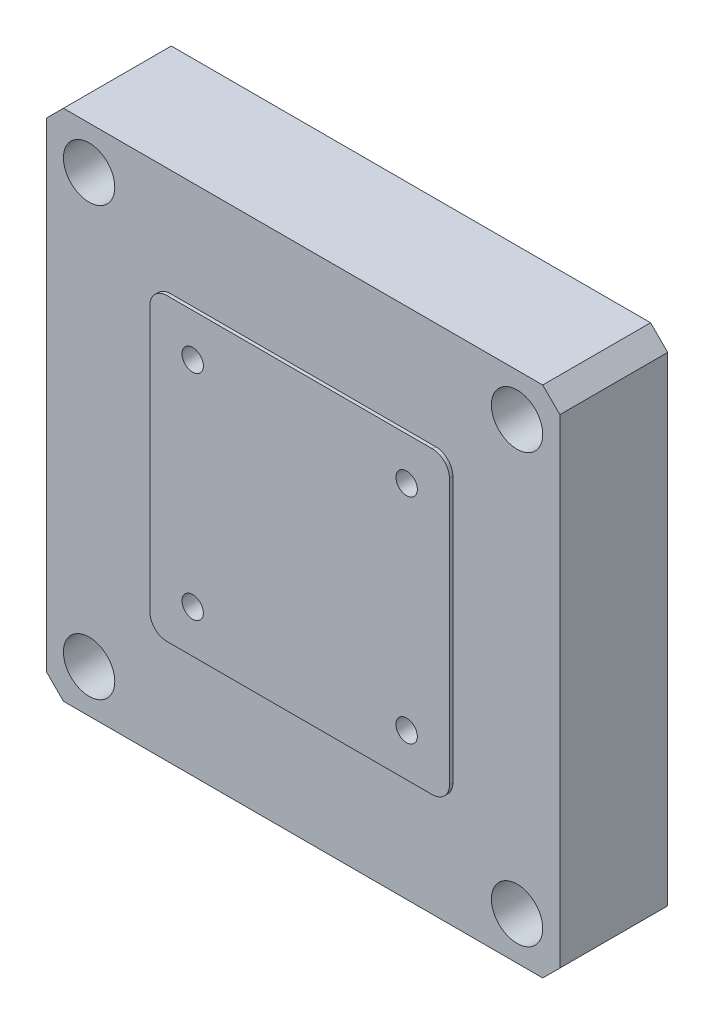
SolidWorks part; units mm, degrees
ref_plane "前视基准面" through (0, 0, 0) normal (0, 0, 1) x (1, 0, 0)
ref_plane "上视基准面" through (0, 0, 0) normal (0, 1, 0) x (1, 0, 0)
ref_plane "右视基准面" through (0, 0, 0) normal (1, 0, 0) x (0, 0, -1)
sketch "草图1" plane through (0, 0, 0) normal (0, 0, 1) x (1, 0, 0)
  line L1 (-30, 30) -> (30, 30)
  line L2 (-30, 30) -> (-30, -30)
  line L3 (-30, -30) -> (30, -30)
  line L4 (30, 30) -> (30, -30)
  line L5 (-30, 30) -> (30, -30) construction
  line L6 (-30, -30) -> (30, 30) construction
  point P0 (0, 0)
  dimension "D1" = 60
extrude "凸台-拉伸1" add sketch "草图1" along normal blind 12.6
chamfer "倒角1" distance 2 angle 45 4 edges at (-30, -30, 6.3) (30, -30, 6.3) (30, 30, 6.3) (-30, 30, 6.3)
sketch "草图2" plane through (0, 0, 12.6) normal (0, 0, 1) x (1, 0, 0)
  line L1 (-17.5, 17.5) -> (17.5, 17.5)
  line L2 (-17.5, 17.5) -> (-17.5, -17.5)
  line L3 (-17.5, -17.5) -> (17.5, -17.5)
  line L4 (17.5, 17.5) -> (17.5, -17.5)
  line L5 (-17.5, 17.5) -> (17.5, -17.5) construction
  line L6 (-17.5, -17.5) -> (17.5, 17.5) construction
  point P0 (0, 0)
  dimension "D1" = 35
extrude "凸台-拉伸2" add sketch "草图2" along normal blind 0.4
fillet "圆角1" radius 2 4 edges at (17.5, -17.5, 12.8) (-17.5, -17.5, 12.8) (17.5, 17.5, 12.8) (-17.5, 17.5, 12.8)
sketch "草图3" plane through (0, 0, 12.6) normal (0, 0, 1) x (1, 0, 0)
  line L1 (-25, 25) -> (25, 25) construction
  line L2 (-25, 25) -> (-25, -25) construction
  line L3 (-25, -25) -> (25, -25) construction
  line L4 (25, 25) -> (25, -25) construction
  line L5 (-25, 25) -> (25, -25) construction
  line L6 (-25, -25) -> (25, 25) construction
  point P0 (0, 0)
  dimension "D1" = 50
sketch "草图4" plane through (0, 0, 13) normal (0, 0, 1) x (1, 0, 0)
  line L0 (-25, -25) -> (25, 25) construction
  line L1 (-12.5, -12.5) -> (12.5, -12.5) construction
  line L2 (-12.5, -12.5) -> (-12.5, 12.5) construction
  line L3 (-12.5, 12.5) -> (12.5, 12.5) construction
  line L4 (12.5, -12.5) -> (12.5, 12.5) construction
  line L5 (-12.5, -12.5) -> (12.5, 12.5) construction
  line L6 (-12.5, 12.5) -> (12.5, -12.5) construction
  point P0 (0, 0)
  dimension "D1" = 25
hole_wizard "孔1" positions "3D草图1" profile "草图5" legacy end condition through all
sketch3d "3D草图1"
  point P0 (-25, 25, 12.6)
  point P3 (25, 25, 12.6)
  point P6 (-25, -25, 12.6)
  point P9 (25, -25, 12.6)
sketch "草图5" plane through (-25, 25, 12.6) normal (1, 0, 0) x (0, -1, 0)
  line L0 (0, 0) -> (0, 12.6)
  line L1 (0, 12.6) -> (1.7, 12.6)
  line L2 (1.7, 12.6) -> (1.7, 5)
  line L3 (1.7, 5) -> (3, 5)
  line L4 (3, 5) -> (3, 0)
  line L5 (3, 0) -> (0, 0)
  line L6 (0, 110) -> (0, -10) construction
  dimension "直径" = 3.4
  dimension "深度" = 12.6
  dimension "柱坑直径" = 6
  dimension "柱坑深度" = 5
hole_wizard "M3 螺纹孔1" positions "3D草图2" profile "草图6" tap size "M3" standard "ISO"
sketch3d "3D草图2"
  point P0 (-12.5, 12.5, 13)
  point P3 (12.5, 12.5, 13)
  point P6 (12.5, -12.5, 13)
  point P9 (-12.5, -12.5, 13)
sketch "草图6" plane through (-12.5, 12.5, 13) normal (1, 0, 0) x (0, -1, 0)
  line L0 (0, 0) -> (0, 4.2511)
  line L1 (0, 4.2511) -> (1.25, 3.5)
  line L2 (1.25, 3.5) -> (1.25, 0)
  line L5 (1.25, 0) -> (0, 0)
  line L10 (0, 4.2511) -> (-1.25, 3.5) construction
  line L11 (0, -6.35) -> (0, 107.95) construction
  dimension "螺纹孔钻头直径" = 2.5
  dimension "螺纹孔钻头深度" = 3.5
  dimension "导头角度" = 118
cosmetic thread "孔螺蚊线1" parameters "D1"=3.5, "D2"=3
cosmetic thread "孔螺蚊线2" parameters "D1"=3.5, "D2"=3
cosmetic thread "孔螺蚊线3" parameters "D1"=3.5, "D2"=3
cosmetic thread "孔螺蚊线4" parameters "D1"=3.5, "D2"=3
sketch "草图7" plane through (0, -30, 0) normal (0, -1, 0) x (1, 0, 0)
  line L0 (-28, 0) -> (28, 0) construction
  line L1 (-30, 0) -> (-30, 12.6) construction
  circle A0 centre (-18.5, 5) radius 2.5
  dimension "D1" = 5
  dimension "D2" = 11.5
  dimension "D3" = 5
